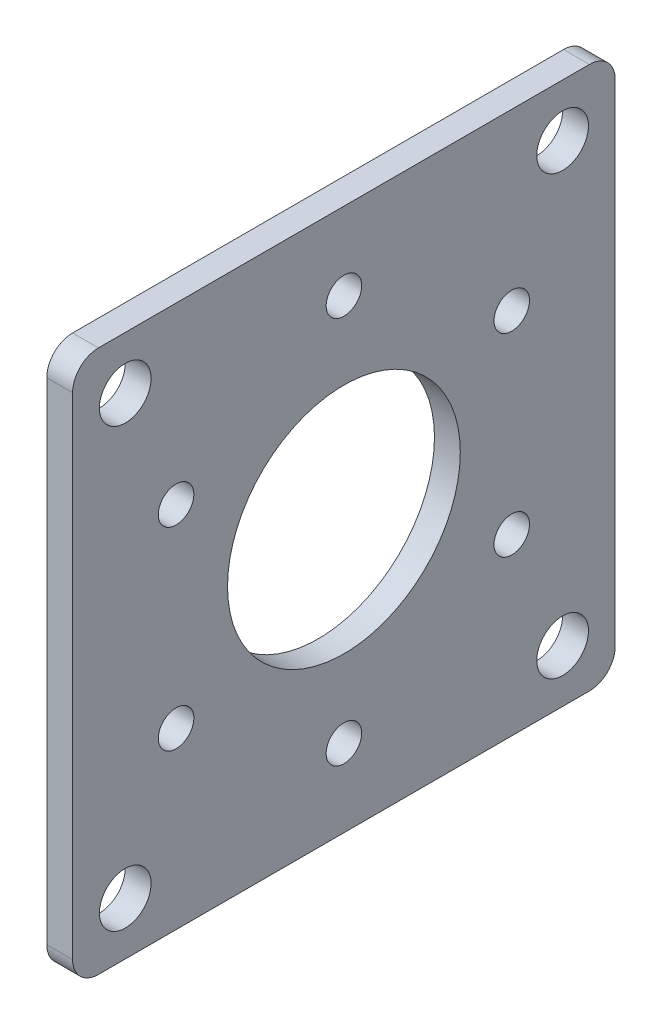
SolidWorks part; units mm, degrees
ref_plane "Front Plane" through (0, 0, 0) normal (0, 0, 1) x (1, 0, 0)
ref_plane "Top Plane" through (0, 0, 0) normal (0, 1, 0) x (1, 0, 0)
ref_plane "Right Plane" through (0, 0, 0) normal (1, 0, 0) x (0, 0, -1)
sketch "Sketch1" plane through (0, 0, 0) normal (1, 0, 0) x (0, 0, -1)
  line L0 (0, 27.4963) -> (0, 23.8125) construction
  line L1 (-33.3375, 33.3375) -> (33.3375, 33.3375)
  line L2 (-33.3375, 33.3375) -> (-33.3375, -33.3375)
  line L3 (-33.3375, -33.3375) -> (33.3375, -33.3375)
  line L4 (33.3375, 33.3375) -> (33.3375, -33.3375)
  line L5 (-33.3375, 33.3375) -> (33.3375, -33.3375) construction
  line L6 (-33.3375, -33.3375) -> (33.3375, 33.3375) construction
  line L7 (0, -27.4963) -> (23.8125, -13.7482) construction
  line L8 (23.8125, -13.7482) -> (23.8125, 13.7482) construction
  line L9 (23.8125, 13.7482) -> (0, 27.4963) construction
  line L10 (0, 27.4963) -> (-23.8125, 13.7482) construction
  line L11 (-23.8125, 13.7482) -> (-23.8125, -13.7482) construction
  line L12 (-23.8125, -13.7482) -> (0, -27.4963) construction
  line L13 (23.8125, 13.7482) -> (20.6222, 11.9063) construction
  line L14 (23.8125, -13.7482) -> (20.6222, -11.9062) construction
  line L15 (-23.8125, -13.7482) -> (-20.6222, -11.9062) construction
  line L16 (-23.8125, 13.7482) -> (-20.6222, 11.9063) construction
  line L17 (0, -27.4963) -> (0, -23.8125) construction
  circle A0 centre (0, 0) radius 38 construction
  circle A1 centre (-26.8701, 26.8701) radius 3.175
  circle A2 centre (26.8701, 26.8701) radius 3.175
  circle A3 centre (26.8701, -26.8701) radius 3.175
  circle A4 centre (-26.8701, -26.8701) radius 3.175
  circle A5 centre (0, 0) radius 14.3002
  circle A7 centre (0, 0) radius 23.8125 construction
  circle A8 centre (0, 23.8125) radius 2.1828
  circle A9 centre (20.6222, 11.9063) radius 2.1828
  circle A10 centre (20.6222, -11.9062) radius 2.1828
  circle A11 centre (0, -23.8125) radius 2.1828
  circle A12 centre (-20.6222, -11.9062) radius 2.1828
  circle A13 centre (-20.6222, 11.9063) radius 2.1828
  point P0 (0, 0)
  dimension "D1" = 76
  dimension "D3" = 6.35
  dimension "D4" = 28.6004
  dimension "D5" = 47.625
  dimension "D6" = 4.3656
  dimension "D2" = 66.675
extrude "Boss-Extrude1" add sketch "Sketch1" along normal blind 3.175
fillet "Fillet1" radius 3.175 4 edges at (1.5875, 33.3375, -33.3375) (1.5875, -33.3375, -33.3375) (1.5875, -33.3375, 33.3375) (1.5875, 33.3375, 33.3375)
